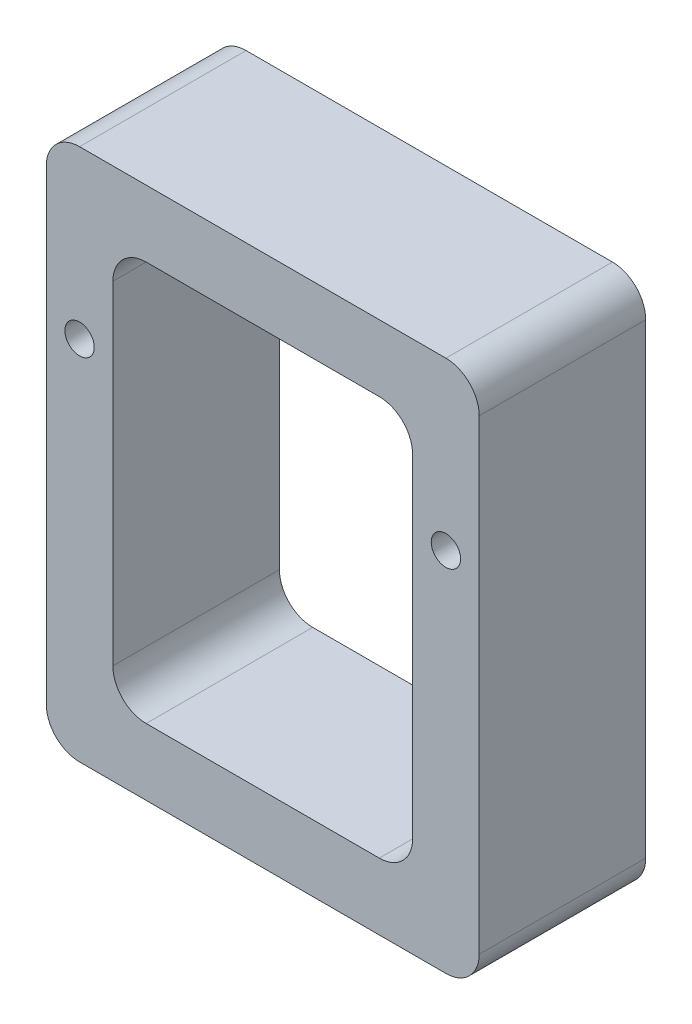
SolidWorks part; units mm, degrees
material "Pink Foam"
ref_plane "Front Plane" through (0, 0, 0) normal (0, 0, 1) x (1, 0, 0)
ref_plane "Top Plane" through (0, 0, 0) normal (0, 1, 0) x (1, 0, 0)
ref_plane "Right Plane" through (0, 0, 0) normal (1, 0, 0) x (0, 0, -1)
sketch "Sketch1" plane through (0, 0, 0) normal (0, 0, 1) x (1, 0, 0)
  line L0 (-114.3, -127) -> (-114.3, 127)
  line L1 (-139.7, -203.2) -> (139.7, -203.2)
  line L2 (-165.1, -177.8) -> (-165.1, 177.8)
  line L3 (-139.7, 203.2) -> (139.7, 203.2)
  line L4 (165.1, -177.8) -> (165.1, 177.8)
  line L5 (-165.1, -203.2) -> (165.1, 203.2) construction
  line L6 (-165.1, 203.2) -> (165.1, -203.2) construction
  line L7 (-88.9, 152.4) -> (88.9, 152.4)
  line L8 (114.3, -127) -> (114.3, 127)
  line L9 (-88.9, -152.4) -> (88.9, -152.4)
  line L10 (114.3, -152.4) -> (114.3, 152.4) construction
  line L11 (-114.3, -152.4) -> (114.3, -152.4) construction
  line L12 (-114.3, 152.4) -> (114.3, 152.4) construction
  line L13 (-114.3, -152.4) -> (-114.3, 152.4) construction
  line L14 (-165.1, -203.2) -> (165.1, -203.2) construction
  line L15 (-165.1, -203.2) -> (-165.1, 203.2) construction
  line L16 (165.1, -203.2) -> (165.1, 203.2) construction
  line L17 (-165.1, 203.2) -> (165.1, 203.2) construction
  line L18 (0, 0) -> (0, 152.4) construction
  line L19 (-114.3, 76.2) -> (-139.7, 76.2) construction
  line L20 (-139.7, 76.2) -> (-165.1, 76.2) construction
  line L21 (114.3, 76.2) -> (139.7, 76.2) construction
  line L22 (139.7, 76.2) -> (165.1, 76.2) construction
  arc A0 (114.3, -127) -> (88.9, -152.4) centre (88.9, -127) cw
  arc A1 (88.9, 152.4) -> (114.3, 127) centre (88.9, 127) cw
  arc A2 (-114.3, 127) -> (-88.9, 152.4) centre (-88.9, 127) cw
  arc A3 (-114.3, -127) -> (-88.9, -152.4) centre (-88.9, -127) ccw
  arc A4 (-139.7, -203.2) -> (-165.1, -177.8) centre (-139.7, -177.8) cw
  arc A5 (139.7, -203.2) -> (165.1, -177.8) centre (139.7, -177.8) ccw
  arc A6 (139.7, 203.2) -> (165.1, 177.8) centre (139.7, 177.8) cw
  arc A7 (-165.1, 177.8) -> (-139.7, 203.2) centre (-139.7, 177.8) cw
  circle A8 centre (-139.7, 76.2) radius 11.2
  circle A9 centre (139.7, 76.2) radius 11.2
  point P0 (0, 0)
  dimension "D4" = 25.4
  dimension "D5" = 22.4
  dimension "D1" = 279.4
  dimension "D2" = 406.4
  dimension "D6" = 76.2
  dimension "D3" = 50.8
extrude "Boss-Extrude1" add sketch "Sketch1" along normal blind 127
